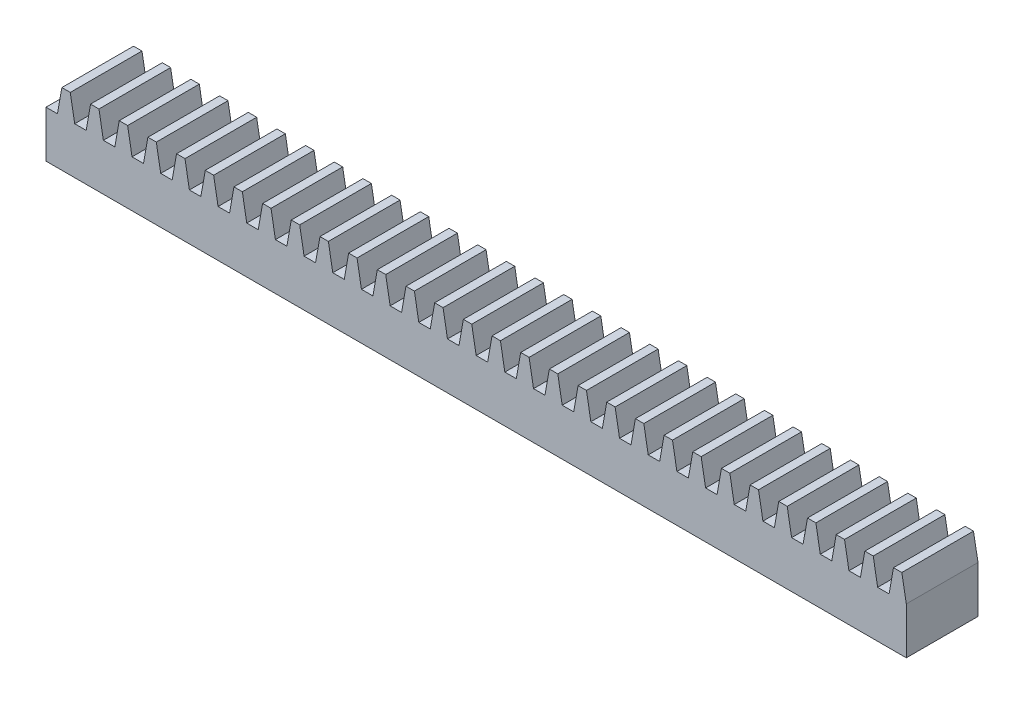
SolidWorks part; units mm, degrees
ref_plane "Front Plane" through (0, 0, 0) normal (0, 0, 1) x (1, 0, 0)
ref_plane "Top Plane" through (0, 0, 0) normal (0, 1, 0) x (1, 0, 0)
ref_plane "Right Plane" through (0, 0, 0) normal (1, 0, 0) x (0, 0, -1)
sketch "Sketch1" plane through (0, 0, 0) normal (1, 0, 0) x (0, 0, -1)
  line L1 (0, 0) -> (6.35, 0)
  line L2 (0, 0) -> (0, 6.35)
  line L3 (0, 6.35) -> (6.35, 6.35)
  line L4 (6.35, 0) -> (6.35, 6.35)
  dimension "D1" = 6.35
  dimension "D2" = 6.35
extrude "Boss-Extrude1" add sketch "Sketch1" against normal blind 76.2
sketch "Sketch2" plane through (0, 0, 0) normal (0, 0, 1) x (1, 0, 0)
  line L0 (0, 6.35) -> (0, 0) construction
  line L1 (-5.08, 4.1402) -> (-5.4696, 6.35)
  line L2 (-4.064, 4.1402) -> (-5.08, 4.1402)
  line L3 (-4.064, 4.1402) -> (-3.6744, 6.35)
  line L4 (-5.4696, 6.35) -> (-3.6744, 6.35)
  line L5 (-1.524, 4.1402) -> (-1.1344, 6.35)
  line L6 (-2.54, 4.1402) -> (-2.9296, 6.35)
  line L7 (-2.9296, 6.35) -> (-1.1344, 6.35)
  line L8 (-7.62, 4.1402) -> (-8.0096, 6.35)
  line L9 (-1.524, 4.1402) -> (-2.54, 4.1402)
  line L10 (-6.604, 4.1402) -> (-7.62, 4.1402)
  line L11 (-6.604, 4.1402) -> (-6.2144, 6.35)
  line L12 (-8.0096, 6.35) -> (-6.2144, 6.35)
  line L13 (-10.16, 4.1402) -> (-10.5496, 6.35)
  line L14 (-9.144, 4.1402) -> (-10.16, 4.1402)
  line L15 (-9.144, 4.1402) -> (-8.7544, 6.35)
  line L16 (-10.5496, 6.35) -> (-8.7544, 6.35)
  line L17 (-12.7, 4.1402) -> (-13.0896, 6.35)
  line L18 (-11.684, 4.1402) -> (-12.7, 4.1402)
  line L19 (-11.684, 4.1402) -> (-11.2944, 6.35)
  line L20 (-13.0896, 6.35) -> (-11.2944, 6.35)
  line L21 (-15.24, 4.1402) -> (-15.6296, 6.35)
  line L22 (-14.224, 4.1402) -> (-15.24, 4.1402)
  line L23 (-14.224, 4.1402) -> (-13.8344, 6.35)
  line L24 (-15.6296, 6.35) -> (-13.8344, 6.35)
  line L25 (-17.78, 4.1402) -> (-18.1696, 6.35)
  line L26 (-16.764, 4.1402) -> (-17.78, 4.1402)
  line L27 (-16.764, 4.1402) -> (-16.3744, 6.35)
  line L28 (-18.1696, 6.35) -> (-16.3744, 6.35)
  line L29 (-20.32, 4.1402) -> (-20.7096, 6.35)
  line L30 (-19.304, 4.1402) -> (-20.32, 4.1402)
  line L31 (-19.304, 4.1402) -> (-18.9144, 6.35)
  line L32 (-20.7096, 6.35) -> (-18.9144, 6.35)
  line L33 (-22.86, 4.1402) -> (-23.2496, 6.35)
  line L34 (-21.844, 4.1402) -> (-22.86, 4.1402)
  line L35 (-21.844, 4.1402) -> (-21.4544, 6.35)
  line L36 (-23.2496, 6.35) -> (-21.4544, 6.35)
  line L37 (-25.4, 4.1402) -> (-25.7896, 6.35)
  line L38 (-24.384, 4.1402) -> (-25.4, 4.1402)
  line L39 (-24.384, 4.1402) -> (-23.9944, 6.35)
  line L40 (-25.7896, 6.35) -> (-23.9944, 6.35)
  line L41 (-27.94, 4.1402) -> (-28.3296, 6.35)
  line L42 (-26.924, 4.1402) -> (-27.94, 4.1402)
  line L43 (-26.924, 4.1402) -> (-26.5344, 6.35)
  line L44 (-28.3296, 6.35) -> (-26.5344, 6.35)
  line L45 (-30.48, 4.1402) -> (-30.8696, 6.35)
  line L46 (-29.464, 4.1402) -> (-30.48, 4.1402)
  line L47 (-29.464, 4.1402) -> (-29.0744, 6.35)
  line L48 (-30.8696, 6.35) -> (-29.0744, 6.35)
  line L49 (-33.02, 4.1402) -> (-33.4096, 6.35)
  line L50 (-32.004, 4.1402) -> (-33.02, 4.1402)
  line L51 (-32.004, 4.1402) -> (-31.6144, 6.35)
  line L52 (-33.4096, 6.35) -> (-31.6144, 6.35)
  line L53 (-35.56, 4.1402) -> (-35.9496, 6.35)
  line L54 (-34.544, 4.1402) -> (-35.56, 4.1402)
  line L55 (-34.544, 4.1402) -> (-34.1544, 6.35)
  line L56 (-35.9496, 6.35) -> (-34.1544, 6.35)
  line L57 (-38.1, 4.1402) -> (-38.4896, 6.35)
  line L58 (-37.084, 4.1402) -> (-38.1, 4.1402)
  line L59 (-37.084, 4.1402) -> (-36.6944, 6.35)
  line L60 (-38.4896, 6.35) -> (-36.6944, 6.35)
  line L61 (-40.64, 4.1402) -> (-41.0296, 6.35)
  line L62 (-39.624, 4.1402) -> (-40.64, 4.1402)
  line L63 (-39.624, 4.1402) -> (-39.2344, 6.35)
  line L64 (-41.0296, 6.35) -> (-39.2344, 6.35)
  line L65 (-43.18, 4.1402) -> (-43.5696, 6.35)
  line L66 (-42.164, 4.1402) -> (-43.18, 4.1402)
  line L67 (-42.164, 4.1402) -> (-41.7744, 6.35)
  line L68 (-43.5696, 6.35) -> (-41.7744, 6.35)
  line L69 (-45.72, 4.1402) -> (-46.1096, 6.35)
  line L70 (-44.704, 4.1402) -> (-45.72, 4.1402)
  line L71 (-44.704, 4.1402) -> (-44.3144, 6.35)
  line L72 (-46.1096, 6.35) -> (-44.3144, 6.35)
  line L73 (-48.26, 4.1402) -> (-48.6496, 6.35)
  line L74 (-47.244, 4.1402) -> (-48.26, 4.1402)
  line L75 (-47.244, 4.1402) -> (-46.8544, 6.35)
  line L76 (-48.6496, 6.35) -> (-46.8544, 6.35)
  line L77 (-50.8, 4.1402) -> (-51.1896, 6.35)
  line L78 (-49.784, 4.1402) -> (-50.8, 4.1402)
  line L79 (-49.784, 4.1402) -> (-49.3944, 6.35)
  line L80 (-51.1896, 6.35) -> (-49.3944, 6.35)
  line L81 (-53.34, 4.1402) -> (-53.7296, 6.35)
  line L82 (-52.324, 4.1402) -> (-53.34, 4.1402)
  line L83 (-52.324, 4.1402) -> (-51.9344, 6.35)
  line L84 (-53.7296, 6.35) -> (-51.9344, 6.35)
  line L85 (-55.88, 4.1402) -> (-56.2696, 6.35)
  line L86 (-54.864, 4.1402) -> (-55.88, 4.1402)
  line L87 (-54.864, 4.1402) -> (-54.4744, 6.35)
  line L88 (-56.2696, 6.35) -> (-54.4744, 6.35)
  line L89 (-58.42, 4.1402) -> (-58.8096, 6.35)
  line L90 (-57.404, 4.1402) -> (-58.42, 4.1402)
  line L91 (-57.404, 4.1402) -> (-57.0144, 6.35)
  line L92 (-58.8096, 6.35) -> (-57.0144, 6.35)
  line L93 (-60.96, 4.1402) -> (-61.3496, 6.35)
  line L94 (-59.944, 4.1402) -> (-60.96, 4.1402)
  line L95 (-59.944, 4.1402) -> (-59.5544, 6.35)
  line L96 (-61.3496, 6.35) -> (-59.5544, 6.35)
  line L97 (-63.5, 4.1402) -> (-63.8896, 6.35)
  line L98 (-62.484, 4.1402) -> (-63.5, 4.1402)
  line L99 (-62.484, 4.1402) -> (-62.0944, 6.35)
  line L100 (-63.8896, 6.35) -> (-62.0944, 6.35)
  line L101 (-66.04, 4.1402) -> (-66.4296, 6.35)
  line L102 (-65.024, 4.1402) -> (-66.04, 4.1402)
  line L103 (-65.024, 4.1402) -> (-64.6344, 6.35)
  line L104 (-66.4296, 6.35) -> (-64.6344, 6.35)
  line L105 (-68.58, 4.1402) -> (-68.9696, 6.35)
  line L106 (-67.564, 4.1402) -> (-68.58, 4.1402)
  line L107 (-67.564, 4.1402) -> (-67.1744, 6.35)
  line L108 (-68.9696, 6.35) -> (-67.1744, 6.35)
  line L109 (-71.12, 4.1402) -> (-71.5096, 6.35)
  line L110 (-70.104, 4.1402) -> (-71.12, 4.1402)
  line L111 (-70.104, 4.1402) -> (-69.7144, 6.35)
  line L112 (-71.5096, 6.35) -> (-69.7144, 6.35)
  line L113 (-73.66, 4.1402) -> (-74.0496, 6.35)
  line L114 (-72.644, 4.1402) -> (-73.66, 4.1402)
  line L115 (-72.644, 4.1402) -> (-72.2544, 6.35)
  line L116 (-74.0496, 6.35) -> (-72.2544, 6.35)
  line L117 (-76.2, 4.1402) -> (-76.5896, 6.35)
  line L118 (-75.184, 4.1402) -> (-76.2, 4.1402)
  line L119 (-75.184, 4.1402) -> (-74.7944, 6.35)
  line L120 (-76.5896, 6.35) -> (-74.7944, 6.35)
  line L121 (-78.74, 4.1402) -> (-79.1296, 6.35)
  line L122 (-77.724, 4.1402) -> (-78.74, 4.1402)
  line L123 (-77.724, 4.1402) -> (-77.3344, 6.35)
  line L124 (-79.1296, 6.35) -> (-77.3344, 6.35)
  line L125 (-81.28, 4.1402) -> (-81.6696, 6.35)
  line L126 (-80.264, 4.1402) -> (-81.28, 4.1402)
  line L127 (-80.264, 4.1402) -> (-79.8744, 6.35)
  line L128 (-81.6696, 6.35) -> (-79.8744, 6.35)
  line L129 (-83.82, 4.1402) -> (-84.2096, 6.35)
  line L130 (-82.804, 4.1402) -> (-83.82, 4.1402)
  line L131 (-82.804, 4.1402) -> (-82.4144, 6.35)
  line L132 (-84.2096, 6.35) -> (-82.4144, 6.35)
  line L133 (-86.36, 4.1402) -> (-86.7496, 6.35)
  line L134 (-85.344, 4.1402) -> (-86.36, 4.1402)
  line L135 (-85.344, 4.1402) -> (-84.9544, 6.35)
  line L136 (-86.7496, 6.35) -> (-84.9544, 6.35)
  line L137 (-88.9, 4.1402) -> (-89.2896, 6.35)
  line L138 (-87.884, 4.1402) -> (-88.9, 4.1402)
  line L139 (-87.884, 4.1402) -> (-87.4944, 6.35)
  line L140 (-89.2896, 6.35) -> (-87.4944, 6.35)
  line L141 (-91.44, 4.1402) -> (-91.8296, 6.35)
  line L142 (-90.424, 4.1402) -> (-91.44, 4.1402)
  line L143 (-90.424, 4.1402) -> (-90.0344, 6.35)
  line L144 (-91.8296, 6.35) -> (-90.0344, 6.35)
  line L145 (-93.98, 4.1402) -> (-94.3696, 6.35)
  line L146 (-92.964, 4.1402) -> (-93.98, 4.1402)
  line L147 (-92.964, 4.1402) -> (-92.5744, 6.35)
  line L148 (-94.3696, 6.35) -> (-92.5744, 6.35)
  line L149 (-96.52, 4.1402) -> (-96.9096, 6.35)
  line L150 (-95.504, 4.1402) -> (-96.52, 4.1402)
  line L151 (-95.504, 4.1402) -> (-95.1144, 6.35)
  line L152 (-96.9096, 6.35) -> (-95.1144, 6.35)
  line L153 (-99.06, 4.1402) -> (-99.4496, 6.35)
  line L154 (-98.044, 4.1402) -> (-99.06, 4.1402)
  line L155 (-98.044, 4.1402) -> (-97.6544, 6.35)
  line L156 (-99.4496, 6.35) -> (-97.6544, 6.35)
  line L157 (-101.6, 4.1402) -> (-101.9896, 6.35)
  line L158 (-100.584, 4.1402) -> (-101.6, 4.1402)
  line L159 (-100.584, 4.1402) -> (-100.1944, 6.35)
  line L160 (-101.9896, 6.35) -> (-100.1944, 6.35)
  line L161 (-104.14, 4.1402) -> (-104.5296, 6.35)
  line L162 (-103.124, 4.1402) -> (-104.14, 4.1402)
  line L163 (-103.124, 4.1402) -> (-102.7344, 6.35)
  line L164 (-104.5296, 6.35) -> (-102.7344, 6.35)
  line L165 (-106.68, 4.1402) -> (-107.0696, 6.35)
  line L166 (-105.664, 4.1402) -> (-106.68, 4.1402)
  line L167 (-105.664, 4.1402) -> (-105.2744, 6.35)
  line L168 (-107.0696, 6.35) -> (-105.2744, 6.35)
  line L169 (-109.22, 4.1402) -> (-109.6096, 6.35)
  line L170 (-108.204, 4.1402) -> (-109.22, 4.1402)
  line L171 (-108.204, 4.1402) -> (-107.8144, 6.35)
  line L172 (-109.6096, 6.35) -> (-107.8144, 6.35)
  line L173 (-111.76, 4.1402) -> (-112.1496, 6.35)
  line L174 (-110.744, 4.1402) -> (-111.76, 4.1402)
  line L175 (-110.744, 4.1402) -> (-110.3544, 6.35)
  line L176 (-112.1496, 6.35) -> (-110.3544, 6.35)
  line L177 (-114.3, 4.1402) -> (-114.6896, 6.35)
  line L178 (-113.284, 4.1402) -> (-114.3, 4.1402)
  line L179 (-113.284, 4.1402) -> (-112.8944, 6.35)
  line L180 (-114.6896, 6.35) -> (-112.8944, 6.35)
  line L181 (-116.84, 4.1402) -> (-117.2296, 6.35)
  line L182 (-115.824, 4.1402) -> (-116.84, 4.1402)
  line L183 (-115.824, 4.1402) -> (-115.4344, 6.35)
  line L184 (-117.2296, 6.35) -> (-115.4344, 6.35)
  line L185 (-119.38, 4.1402) -> (-119.7696, 6.35)
  line L186 (-118.364, 4.1402) -> (-119.38, 4.1402)
  line L187 (-118.364, 4.1402) -> (-117.9744, 6.35)
  line L188 (-119.7696, 6.35) -> (-117.9744, 6.35)
  line L189 (-121.92, 4.1402) -> (-122.3096, 6.35)
  line L190 (-120.904, 4.1402) -> (-121.92, 4.1402)
  line L191 (-120.904, 4.1402) -> (-120.5144, 6.35)
  line L192 (-122.3096, 6.35) -> (-120.5144, 6.35)
  line L193 (-124.46, 4.1402) -> (-124.8496, 6.35)
  line L194 (-123.444, 4.1402) -> (-124.46, 4.1402)
  line L195 (-123.444, 4.1402) -> (-123.0544, 6.35)
  line L196 (-124.8496, 6.35) -> (-123.0544, 6.35)
  line L197 (-127, 4.1402) -> (-127.3896, 6.35)
  line L198 (-125.984, 4.1402) -> (-127, 4.1402)
  line L199 (-125.984, 4.1402) -> (-125.5944, 6.35)
  line L200 (-127.3896, 6.35) -> (-125.5944, 6.35)
  line L201 (-129.54, 4.1402) -> (-129.9296, 6.35)
  line L202 (-128.524, 4.1402) -> (-129.54, 4.1402)
  line L203 (-128.524, 4.1402) -> (-128.1344, 6.35)
  line L204 (-129.9296, 6.35) -> (-128.1344, 6.35)
  line L205 (-132.08, 4.1402) -> (-132.4696, 6.35)
  line L206 (-131.064, 4.1402) -> (-132.08, 4.1402)
  line L207 (-131.064, 4.1402) -> (-130.6744, 6.35)
  line L208 (-132.4696, 6.35) -> (-130.6744, 6.35)
  line L209 (-134.62, 4.1402) -> (-135.0096, 6.35)
  line L210 (-133.604, 4.1402) -> (-134.62, 4.1402)
  line L211 (-133.604, 4.1402) -> (-133.2144, 6.35)
  line L212 (-135.0096, 6.35) -> (-133.2144, 6.35)
  line L213 (-137.16, 4.1402) -> (-137.5496, 6.35)
  line L214 (-136.144, 4.1402) -> (-137.16, 4.1402)
  line L215 (-136.144, 4.1402) -> (-135.7544, 6.35)
  line L216 (-137.5496, 6.35) -> (-135.7544, 6.35)
  line L217 (-139.7, 4.1402) -> (-140.0896, 6.35)
  line L218 (-138.684, 4.1402) -> (-139.7, 4.1402)
  line L219 (-138.684, 4.1402) -> (-138.2944, 6.35)
  line L220 (-140.0896, 6.35) -> (-138.2944, 6.35)
  line L221 (-142.24, 4.1402) -> (-142.6296, 6.35)
  line L222 (-141.224, 4.1402) -> (-142.24, 4.1402)
  line L223 (-141.224, 4.1402) -> (-140.8344, 6.35)
  line L224 (-142.6296, 6.35) -> (-140.8344, 6.35)
  line L225 (-144.78, 4.1402) -> (-145.1696, 6.35)
  line L226 (-143.764, 4.1402) -> (-144.78, 4.1402)
  line L227 (-143.764, 4.1402) -> (-143.3744, 6.35)
  line L228 (-145.1696, 6.35) -> (-143.3744, 6.35)
  line L229 (-147.32, 4.1402) -> (-147.7096, 6.35)
  line L230 (-146.304, 4.1402) -> (-147.32, 4.1402)
  line L231 (-146.304, 4.1402) -> (-145.9144, 6.35)
  line L232 (-147.7096, 6.35) -> (-145.9144, 6.35)
  line L233 (-149.86, 4.1402) -> (-150.2496, 6.35)
  line L234 (-148.844, 4.1402) -> (-149.86, 4.1402)
  line L235 (-148.844, 4.1402) -> (-148.4544, 6.35)
  line L236 (-150.2496, 6.35) -> (-148.4544, 6.35)
  line L237 (-152.4, 4.1402) -> (-152.7896, 6.35)
  line L238 (-151.384, 4.1402) -> (-152.4, 4.1402)
  line L239 (-151.384, 4.1402) -> (-150.9944, 6.35)
  line L240 (-152.7896, 6.35) -> (-150.9944, 6.35)
  line L241 (-154.94, 4.1402) -> (-155.3296, 6.35)
  line L242 (-153.924, 4.1402) -> (-154.94, 4.1402)
  line L243 (-153.924, 4.1402) -> (-153.5344, 6.35)
  line L244 (-155.3296, 6.35) -> (-153.5344, 6.35)
  line L245 (-157.48, 4.1402) -> (-157.8696, 6.35)
  line L246 (-156.464, 4.1402) -> (-157.48, 4.1402)
  line L247 (-156.464, 4.1402) -> (-156.0744, 6.35)
  line L248 (-157.8696, 6.35) -> (-156.0744, 6.35)
  line L249 (-160.02, 4.1402) -> (-160.4096, 6.35)
  line L250 (-159.004, 4.1402) -> (-160.02, 4.1402)
  line L251 (-159.004, 4.1402) -> (-158.6144, 6.35)
  line L252 (-160.4096, 6.35) -> (-158.6144, 6.35)
  line L253 (-162.56, 4.1402) -> (-162.9496, 6.35)
  line L254 (-161.544, 4.1402) -> (-162.56, 4.1402)
  line L255 (-161.544, 4.1402) -> (-161.1544, 6.35)
  line L256 (-162.9496, 6.35) -> (-161.1544, 6.35)
  line L257 (-165.1, 4.1402) -> (-165.4896, 6.35)
  line L258 (-164.084, 4.1402) -> (-165.1, 4.1402)
  line L259 (-164.084, 4.1402) -> (-163.6944, 6.35)
  line L260 (-165.4896, 6.35) -> (-163.6944, 6.35)
  line L261 (-167.64, 4.1402) -> (-168.0296, 6.35)
  line L262 (-166.624, 4.1402) -> (-167.64, 4.1402)
  line L263 (-166.624, 4.1402) -> (-166.2344, 6.35)
  line L264 (-168.0296, 6.35) -> (-166.2344, 6.35)
  line L265 (-170.18, 4.1402) -> (-170.5696, 6.35)
  line L266 (-169.164, 4.1402) -> (-170.18, 4.1402)
  line L267 (-169.164, 4.1402) -> (-168.7744, 6.35)
  line L268 (-170.5696, 6.35) -> (-168.7744, 6.35)
  line L269 (-172.72, 4.1402) -> (-173.1096, 6.35)
  line L270 (-171.704, 4.1402) -> (-172.72, 4.1402)
  line L271 (-171.704, 4.1402) -> (-171.3144, 6.35)
  line L272 (-173.1096, 6.35) -> (-171.3144, 6.35)
  line L273 (-175.26, 4.1402) -> (-175.6496, 6.35)
  line L274 (-174.244, 4.1402) -> (-175.26, 4.1402)
  line L275 (-174.244, 4.1402) -> (-173.8544, 6.35)
  line L276 (-175.6496, 6.35) -> (-173.8544, 6.35)
  line L277 (-177.8, 4.1402) -> (-178.1896, 6.35)
  line L278 (-176.784, 4.1402) -> (-177.8, 4.1402)
  line L279 (-176.784, 4.1402) -> (-176.3944, 6.35)
  line L280 (-178.1896, 6.35) -> (-176.3944, 6.35)
  line L281 (-180.34, 4.1402) -> (-180.7296, 6.35)
  line L282 (-179.324, 4.1402) -> (-180.34, 4.1402)
  line L283 (-179.324, 4.1402) -> (-178.9344, 6.35)
  line L284 (-180.7296, 6.35) -> (-178.9344, 6.35)
  line L285 (-182.88, 4.1402) -> (-183.2696, 6.35)
  line L286 (-181.864, 4.1402) -> (-182.88, 4.1402)
  line L287 (-181.864, 4.1402) -> (-181.4744, 6.35)
  line L288 (-183.2696, 6.35) -> (-181.4744, 6.35)
  line L289 (-185.42, 4.1402) -> (-185.8096, 6.35)
  line L290 (-184.404, 4.1402) -> (-185.42, 4.1402)
  line L291 (-184.404, 4.1402) -> (-184.0144, 6.35)
  line L292 (-185.8096, 6.35) -> (-184.0144, 6.35)
  line L293 (-187.96, 4.1402) -> (-188.3496, 6.35)
  line L294 (-186.944, 4.1402) -> (-187.96, 4.1402)
  line L295 (-186.944, 4.1402) -> (-186.5544, 6.35)
  line L296 (-188.3496, 6.35) -> (-186.5544, 6.35)
  line L297 (-190.5, 4.1402) -> (-190.8896, 6.35)
  line L298 (-189.484, 4.1402) -> (-190.5, 4.1402)
  line L299 (-189.484, 4.1402) -> (-189.0944, 6.35)
  line L300 (-190.8896, 6.35) -> (-189.0944, 6.35)
  line L301 (-193.04, 4.1402) -> (-193.4296, 6.35)
  line L302 (-192.024, 4.1402) -> (-193.04, 4.1402)
  line L303 (-192.024, 4.1402) -> (-191.6344, 6.35)
  line L304 (-193.4296, 6.35) -> (-191.6344, 6.35)
  line L305 (-195.58, 4.1402) -> (-195.9696, 6.35)
  line L306 (-194.564, 4.1402) -> (-195.58, 4.1402)
  line L307 (-194.564, 4.1402) -> (-194.1744, 6.35)
  line L308 (-195.9696, 6.35) -> (-194.1744, 6.35)
  line L309 (-198.12, 4.1402) -> (-198.5096, 6.35)
  line L310 (-197.104, 4.1402) -> (-198.12, 4.1402)
  line L311 (-197.104, 4.1402) -> (-196.7144, 6.35)
  line L312 (-198.5096, 6.35) -> (-196.7144, 6.35)
  line L313 (-200.66, 4.1402) -> (-201.0496, 6.35)
  line L314 (-199.644, 4.1402) -> (-200.66, 4.1402)
  line L315 (-199.644, 4.1402) -> (-199.2544, 6.35)
  line L316 (-201.0496, 6.35) -> (-199.2544, 6.35)
  line L317 (-203.2, 4.1402) -> (-203.5896, 6.35)
  line L318 (-202.184, 4.1402) -> (-203.2, 4.1402)
  line L319 (-202.184, 4.1402) -> (-201.7944, 6.35)
  line L320 (-203.5896, 6.35) -> (-201.7944, 6.35)
  line L321 (-205.74, 4.1402) -> (-206.1296, 6.35)
  line L322 (-204.724, 4.1402) -> (-205.74, 4.1402)
  line L323 (-204.724, 4.1402) -> (-204.3344, 6.35)
  line L324 (-206.1296, 6.35) -> (-204.3344, 6.35)
  line L325 (-208.28, 4.1402) -> (-208.6696, 6.35)
  line L326 (-207.264, 4.1402) -> (-208.28, 4.1402)
  line L327 (-207.264, 4.1402) -> (-206.8744, 6.35)
  line L328 (-208.6696, 6.35) -> (-206.8744, 6.35)
  line L329 (-210.82, 4.1402) -> (-211.2096, 6.35)
  line L330 (-209.804, 4.1402) -> (-210.82, 4.1402)
  line L331 (-209.804, 4.1402) -> (-209.4144, 6.35)
  line L332 (-211.2096, 6.35) -> (-209.4144, 6.35)
  line L333 (-213.36, 4.1402) -> (-213.7496, 6.35)
  line L334 (-212.344, 4.1402) -> (-213.36, 4.1402)
  line L335 (-212.344, 4.1402) -> (-211.9544, 6.35)
  line L336 (-213.7496, 6.35) -> (-211.9544, 6.35)
  line L337 (-215.9, 4.1402) -> (-216.2896, 6.35)
  line L338 (-214.884, 4.1402) -> (-215.9, 4.1402)
  line L339 (-214.884, 4.1402) -> (-214.4944, 6.35)
  line L340 (-216.2896, 6.35) -> (-214.4944, 6.35)
  line L341 (-218.44, 4.1402) -> (-218.8296, 6.35)
  line L342 (-217.424, 4.1402) -> (-218.44, 4.1402)
  line L343 (-217.424, 4.1402) -> (-217.0344, 6.35)
  line L344 (-218.8296, 6.35) -> (-217.0344, 6.35)
  line L345 (-220.98, 4.1402) -> (-221.3696, 6.35)
  line L346 (-219.964, 4.1402) -> (-220.98, 4.1402)
  line L347 (-219.964, 4.1402) -> (-219.5744, 6.35)
  line L348 (-221.3696, 6.35) -> (-219.5744, 6.35)
  line L349 (-223.52, 4.1402) -> (-223.9096, 6.35)
  line L350 (-222.504, 4.1402) -> (-223.52, 4.1402)
  line L351 (-222.504, 4.1402) -> (-222.1144, 6.35)
  line L352 (-223.9096, 6.35) -> (-222.1144, 6.35)
  line L353 (-226.06, 4.1402) -> (-226.4496, 6.35)
  line L354 (-225.044, 4.1402) -> (-226.06, 4.1402)
  line L355 (-225.044, 4.1402) -> (-224.6544, 6.35)
  line L356 (-226.4496, 6.35) -> (-224.6544, 6.35)
  line L357 (-228.6, 4.1402) -> (-228.9896, 6.35)
  line L358 (-227.584, 4.1402) -> (-228.6, 4.1402)
  line L359 (-227.584, 4.1402) -> (-227.1944, 6.35)
  line L360 (-228.9896, 6.35) -> (-227.1944, 6.35)
  line L361 (-231.14, 4.1402) -> (-231.5296, 6.35)
  line L362 (-230.124, 4.1402) -> (-231.14, 4.1402)
  line L363 (-230.124, 4.1402) -> (-229.7344, 6.35)
  line L364 (-231.5296, 6.35) -> (-229.7344, 6.35)
  line L365 (-233.68, 4.1402) -> (-234.0696, 6.35)
  line L366 (-232.664, 4.1402) -> (-233.68, 4.1402)
  line L367 (-232.664, 4.1402) -> (-232.2744, 6.35)
  line L368 (-234.0696, 6.35) -> (-232.2744, 6.35)
  line L369 (-236.22, 4.1402) -> (-236.6096, 6.35)
  line L370 (-235.204, 4.1402) -> (-236.22, 4.1402)
  line L371 (-235.204, 4.1402) -> (-234.8144, 6.35)
  line L372 (-236.6096, 6.35) -> (-234.8144, 6.35)
  line L373 (-238.76, 4.1402) -> (-239.1496, 6.35)
  line L374 (-237.744, 4.1402) -> (-238.76, 4.1402)
  line L375 (-237.744, 4.1402) -> (-237.3544, 6.35)
  line L376 (-239.1496, 6.35) -> (-237.3544, 6.35)
  line L377 (-241.3, 4.1402) -> (-241.6896, 6.35)
  line L378 (-240.284, 4.1402) -> (-241.3, 4.1402)
  line L379 (-240.284, 4.1402) -> (-239.8944, 6.35)
  line L380 (-241.6896, 6.35) -> (-239.8944, 6.35)
  line L381 (-243.84, 4.1402) -> (-244.2296, 6.35)
  line L382 (-242.824, 4.1402) -> (-243.84, 4.1402)
  line L383 (-242.824, 4.1402) -> (-242.4344, 6.35)
  line L384 (-244.2296, 6.35) -> (-242.4344, 6.35)
  line L385 (-246.38, 4.1402) -> (-246.7696, 6.35)
  line L386 (-245.364, 4.1402) -> (-246.38, 4.1402)
  line L387 (-245.364, 4.1402) -> (-244.9744, 6.35)
  line L388 (-246.7696, 6.35) -> (-244.9744, 6.35)
  line L389 (-248.92, 4.1402) -> (-249.3096, 6.35)
  line L390 (-247.904, 4.1402) -> (-248.92, 4.1402)
  line L391 (-247.904, 4.1402) -> (-247.5144, 6.35)
  line L392 (-249.3096, 6.35) -> (-247.5144, 6.35)
  line L393 (-251.46, 4.1402) -> (-251.8496, 6.35)
  line L394 (-250.444, 4.1402) -> (-251.46, 4.1402)
  line L395 (-250.444, 4.1402) -> (-250.0544, 6.35)
  line L396 (-251.8496, 6.35) -> (-250.0544, 6.35)
  line L397 (-254, 4.1402) -> (-254.3896, 6.35)
  line L398 (-252.984, 4.1402) -> (-254, 4.1402)
  line L399 (-252.984, 4.1402) -> (-252.5944, 6.35)
  line L400 (-254.3896, 6.35) -> (-252.5944, 6.35)
  line L401 (-256.54, 4.1402) -> (-256.9296, 6.35)
  line L402 (-255.524, 4.1402) -> (-256.54, 4.1402)
  line L403 (-255.524, 4.1402) -> (-255.1344, 6.35)
  line L404 (-256.9296, 6.35) -> (-255.1344, 6.35)
  line L405 (-259.08, 4.1402) -> (-259.4696, 6.35)
  line L406 (-258.064, 4.1402) -> (-259.08, 4.1402)
  line L407 (-258.064, 4.1402) -> (-257.6744, 6.35)
  line L408 (-259.4696, 6.35) -> (-257.6744, 6.35)
  line L409 (-261.62, 4.1402) -> (-262.0096, 6.35)
  line L410 (-260.604, 4.1402) -> (-261.62, 4.1402)
  line L411 (-260.604, 4.1402) -> (-260.2144, 6.35)
  line L412 (-262.0096, 6.35) -> (-260.2144, 6.35)
  line L413 (-264.16, 4.1402) -> (-264.5496, 6.35)
  line L414 (-263.144, 4.1402) -> (-264.16, 4.1402)
  line L415 (-263.144, 4.1402) -> (-262.7544, 6.35)
  line L416 (-264.5496, 6.35) -> (-262.7544, 6.35)
  line L417 (-266.7, 4.1402) -> (-267.0896, 6.35)
  line L418 (-265.684, 4.1402) -> (-266.7, 4.1402)
  line L419 (-265.684, 4.1402) -> (-265.2944, 6.35)
  line L420 (-267.0896, 6.35) -> (-265.2944, 6.35)
  line L421 (-269.24, 4.1402) -> (-269.6296, 6.35)
  line L422 (-268.224, 4.1402) -> (-269.24, 4.1402)
  line L423 (-268.224, 4.1402) -> (-267.8344, 6.35)
  line L424 (-269.6296, 6.35) -> (-267.8344, 6.35)
  line L425 (-271.78, 4.1402) -> (-272.1696, 6.35)
  line L426 (-270.764, 4.1402) -> (-271.78, 4.1402)
  line L427 (-270.764, 4.1402) -> (-270.3744, 6.35)
  line L428 (-272.1696, 6.35) -> (-270.3744, 6.35)
  line L429 (-274.32, 4.1402) -> (-274.7096, 6.35)
  line L430 (-273.304, 4.1402) -> (-274.32, 4.1402)
  line L431 (-273.304, 4.1402) -> (-272.9144, 6.35)
  line L432 (-274.7096, 6.35) -> (-272.9144, 6.35)
  line L433 (-276.86, 4.1402) -> (-277.2496, 6.35)
  line L434 (-275.844, 4.1402) -> (-276.86, 4.1402)
  line L435 (-275.844, 4.1402) -> (-275.4544, 6.35)
  line L436 (-277.2496, 6.35) -> (-275.4544, 6.35)
  line L437 (-279.4, 4.1402) -> (-279.7896, 6.35)
  line L438 (-278.384, 4.1402) -> (-279.4, 4.1402)
  line L439 (-278.384, 4.1402) -> (-277.9944, 6.35)
  line L440 (-279.7896, 6.35) -> (-277.9944, 6.35)
  line L441 (-281.94, 4.1402) -> (-282.3296, 6.35)
  line L442 (-280.924, 4.1402) -> (-281.94, 4.1402)
  line L443 (-280.924, 4.1402) -> (-280.5344, 6.35)
  line L444 (-282.3296, 6.35) -> (-280.5344, 6.35)
  line L445 (-284.48, 4.1402) -> (-284.8696, 6.35)
  line L446 (-283.464, 4.1402) -> (-284.48, 4.1402)
  line L447 (-283.464, 4.1402) -> (-283.0744, 6.35)
  line L448 (-284.8696, 6.35) -> (-283.0744, 6.35)
  line L449 (-287.02, 4.1402) -> (-287.4096, 6.35)
  line L450 (-286.004, 4.1402) -> (-287.02, 4.1402)
  line L451 (-286.004, 4.1402) -> (-285.6144, 6.35)
  line L452 (-287.4096, 6.35) -> (-285.6144, 6.35)
  line L453 (-289.56, 4.1402) -> (-289.9496, 6.35)
  line L454 (-288.544, 4.1402) -> (-289.56, 4.1402)
  line L455 (-288.544, 4.1402) -> (-288.1544, 6.35)
  line L456 (-289.9496, 6.35) -> (-288.1544, 6.35)
  line L457 (-292.1, 4.1402) -> (-292.4896, 6.35)
  line L458 (-291.084, 4.1402) -> (-292.1, 4.1402)
  line L459 (-291.084, 4.1402) -> (-290.6944, 6.35)
  line L460 (-292.4896, 6.35) -> (-290.6944, 6.35)
  line L461 (-294.64, 4.1402) -> (-295.0296, 6.35)
  line L462 (-293.624, 4.1402) -> (-294.64, 4.1402)
  line L463 (-293.624, 4.1402) -> (-293.2344, 6.35)
  line L464 (-295.0296, 6.35) -> (-293.2344, 6.35)
  line L465 (-297.18, 4.1402) -> (-297.5696, 6.35)
  line L466 (-296.164, 4.1402) -> (-297.18, 4.1402)
  line L467 (-296.164, 4.1402) -> (-295.7744, 6.35)
  line L468 (-297.5696, 6.35) -> (-295.7744, 6.35)
  line L469 (-299.72, 4.1402) -> (-300.1096, 6.35)
  line L470 (-298.704, 4.1402) -> (-299.72, 4.1402)
  line L471 (-298.704, 4.1402) -> (-298.3144, 6.35)
  line L472 (-300.1096, 6.35) -> (-298.3144, 6.35)
  line L473 (-302.26, 4.1402) -> (-302.6496, 6.35)
  line L474 (-301.244, 4.1402) -> (-302.26, 4.1402)
  line L475 (-301.244, 4.1402) -> (-300.8544, 6.35)
  line L476 (-302.6496, 6.35) -> (-300.8544, 6.35)
  line L477 (-304.8, 4.1402) -> (-305.1896, 6.35)
  line L478 (-303.784, 4.1402) -> (-304.8, 4.1402)
  line L479 (-303.784, 4.1402) -> (-303.3944, 6.35)
  line L480 (-305.1896, 6.35) -> (-303.3944, 6.35)
  line L481 (-0.3978, 6.35) -> (0, 6.35)
  line L482 (-0.3978, 6.35) -> (0, 4.1402)
  line L483 (0, 6.35) -> (0, 4.1402)
  dimension "D1" = 1.524
  dimension "D2" = 120
  dimension "D3" = 0.7447
  dimension "D4" = 0.7366
  dimension "D6" = 1.016
extrude "Cut-Extrude1" cut sketch "Sketch2" against normal blind 76.2
sketch "Sketch3" plane through (0, 0, 0) normal (0, -1, 0) x (1, 0, 0)
  line L1 (0, 0) -> (0, -6.35) construction
  circle A1 centre (-19.05, -3.175) radius 1.3462
  dimension "D1" = 19.05
  dimension "D2" = 2.6924
extrude "Cut-Extrude2" cut sketch "Sketch3" against normal blind 4.572
cosmetic thread "Cosmetic Thread1" parameters "D2"=3.5052
